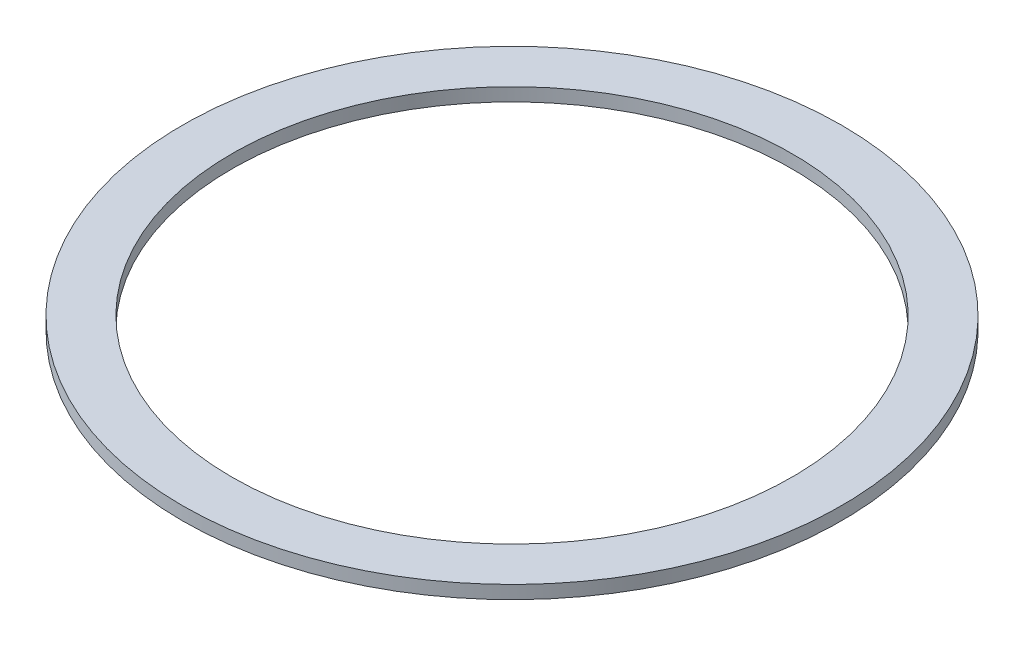
SolidWorks part; units mm, degrees
ref_plane "Plano frontal" through (0, 0, 0) normal (0, 0, 1) x (1, 0, 0)
ref_plane "Plano superior" through (0, 0, 0) normal (0, 1, 0) x (1, 0, 0)
ref_plane "Plano direito" through (0, 0, 0) normal (1, 0, 0) x (0, 0, -1)
sketch "Esboço1" plane through (0, 0, 0) normal (0, 1, 0) x (1, 0, 0)
  circle A0 centre (0, 0) radius 100
  circle A1 centre (0, 0) radius 85
extrude "Ressalto-extrusão1" add sketch "Esboço1" along normal blind 4
